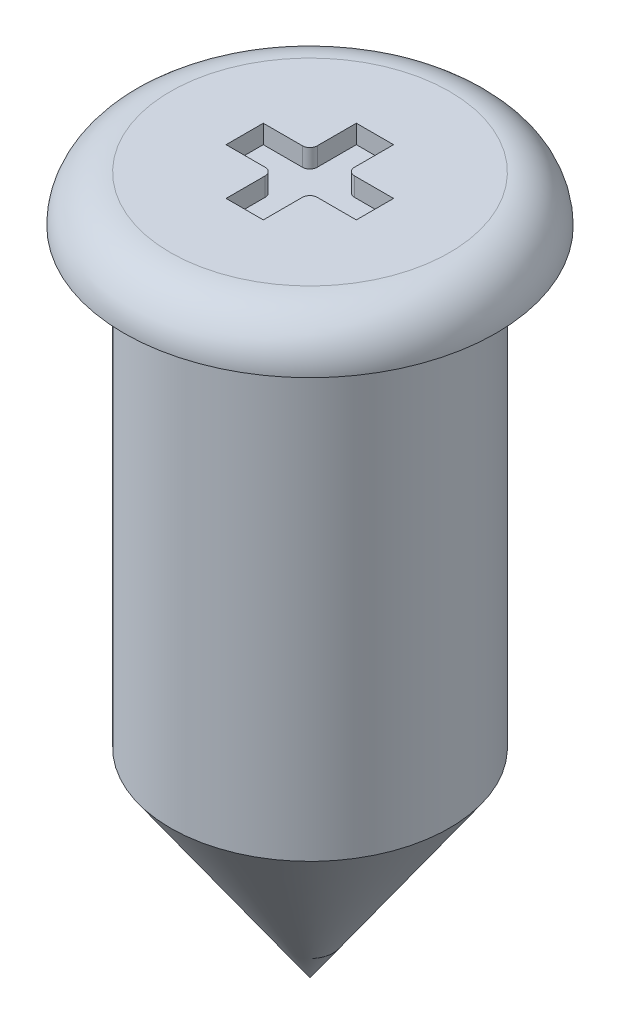
SolidWorks part; units mm, degrees
ref_plane "Front" through (0, 0, 0) normal (0, 0, 1) x (1, 0, 0)
ref_plane "Top" through (0, 0, 0) normal (0, 1, 0) x (1, 0, 0)
ref_plane "Right" through (0, 0, 0) normal (1, 0, 0) x (0, 0, -1)
sketch "Sketch1" plane through (0, 0, 0) normal (0, 0, 1) x (1, 0, 0)
  line L0 (0, -10.656) -> (0, -14.406)
  line L1 (0, -55) -> (0, 55) construction
  line L2 (0.75, -13.3333) -> (0.75, -10.906)
  line L3 (0.75, -10.906) -> (1, -10.906)
  line L4 (0.75, -10.656) -> (0, -10.656)
  line L5 (0, -14.406) -> (0.75, -13.3333)
  arc A0 (1, -10.906) -> (0.75, -10.656) centre (0.75, -10.906) ccw
revolve "Revolve1" add sketch "Sketch1" angle 360 about L0
cosmetic thread "Cosmetic Thread1" parameters "D2"=0.911
sketch "Sketch2" plane through (0, -10.656, 0) normal (0, 1, 0) x (1, 0, 0)
  line L0 (-0.1027, 0.3517) -> (0.0973, 0.3517)
  line L1 (0.0973, 0.3517) -> (0.0973, 0.1417)
  line L2 (0.1373, 0.1017) -> (0.3473, 0.1017)
  line L3 (0.3473, 0.1017) -> (0.3473, -0.0983)
  line L4 (0.3473, -0.0983) -> (0.1373, -0.0983)
  line L5 (0.0973, -0.1383) -> (0.0973, -0.3483)
  line L6 (0.0973, -0.3483) -> (-0.1027, -0.3483)
  line L7 (-0.0027, 0.3517) -> (-0.0027, -0.3483) construction
  line L8 (-0.1027, -0.1383) -> (-0.1027, -0.3483)
  line L9 (-0.3527, -0.0983) -> (-0.1427, -0.0983)
  line L10 (-0.3527, 0.1017) -> (-0.3527, -0.0983)
  line L11 (-0.1427, 0.1017) -> (-0.3527, 0.1017)
  line L12 (-0.1027, 0.3517) -> (-0.1027, 0.1417)
  arc A0 (0.0973, 0.1417) -> (0.1373, 0.1017) centre (0.1373, 0.1417) ccw
  arc A1 (0.1373, -0.0983) -> (0.0973, -0.1383) centre (0.1373, -0.1383) ccw
  arc A2 (-0.1427, -0.0983) -> (-0.1027, -0.1383) centre (-0.1427, -0.1383) cw
  arc A3 (-0.1027, 0.1417) -> (-0.1427, 0.1017) centre (-0.1427, 0.1417) cw
  dimension "D1" = 0.04
  dimension "D2" = 0.04
extrude "Cut-Extrude1" cut sketch "Sketch2" against normal blind 0.1
